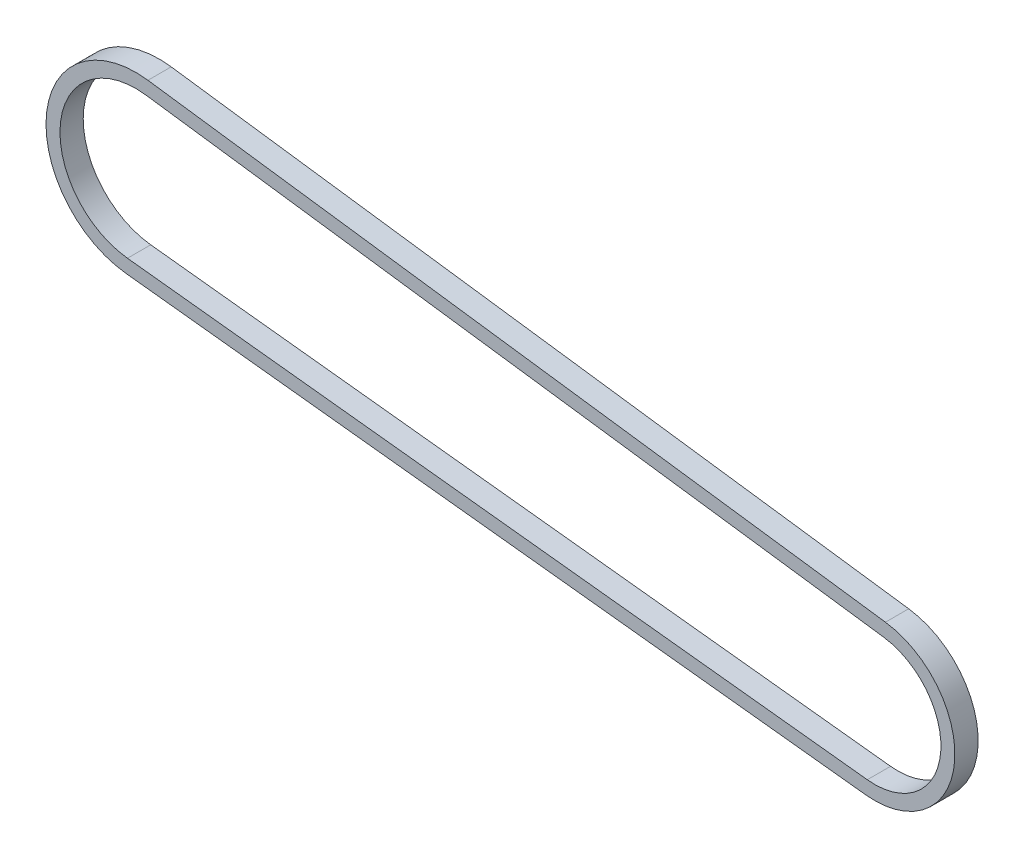
SolidWorks part; units mm, degrees
ref_plane "Front Plane" through (0, 0, 0) normal (0, 0, 1) x (1, 0, 0)
ref_plane "Top Plane" through (0, 0, 0) normal (0, 1, 0) x (1, 0, 0)
ref_plane "Right Plane" through (0, 0, 0) normal (1, 0, 0) x (0, 0, -1)
sketch "Sketch1" plane through (0, 0, 0) normal (0, 0, 1) x (1, 0, 0)
  line L0 (-99.437, 22.6973) -> (1.2234, 8.9721)
  line L1 (-101.9718, 2.1537) -> (-0.9942, -9.0004)
  line L2 (-99.1796, 24.5848) -> (1.4807, 10.8596)
  line L3 (-102.1809, 0.2602) -> (-1.2033, -10.8938)
  arc A0 (1.2234, 8.9721) -> (-0.9942, -9.0004) centre (0, 0) cw
  arc A1 (-99.437, 22.6973) -> (-101.9718, 2.1537) centre (-100.8353, 12.4417) ccw
  arc A4 (1.4807, 10.8596) -> (-1.2033, -10.8938) centre (0, 0) cw
  arc A5 (-99.1796, 24.5848) -> (-102.1809, 0.2602) centre (-100.8353, 12.4417) ccw
  dimension "D1" = 9.0551
  dimension "D2" = 10.3505
  dimension "D3" = 1.905
extrude "Boss-Extrude1" add sketch "Sketch1" along normal blind 3.175
